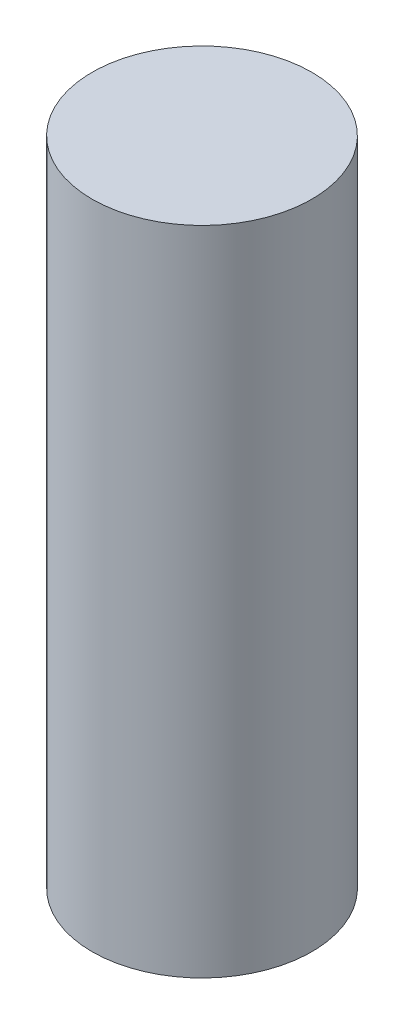
SolidWorks part; units mm, degrees
ref_plane "Front Plane" through (0, 0, 0) normal (0, 0, 1) x (1, 0, 0)
ref_plane "Top Plane" through (0, 0, 0) normal (0, 1, 0) x (1, 0, 0)
ref_plane "Right Plane" through (0, 0, 0) normal (1, 0, 0) x (0, 0, -1)
sketch "Sketch1" plane through (0, 0, 0) normal (0, 1, 0) x (1, 0, 0)
  circle A0 centre (0, 0) radius 7.085
  dimension "D1" = 14.17
extrude "Boss-Extrude1" add sketch "Sketch1" along normal blind 42.0116
